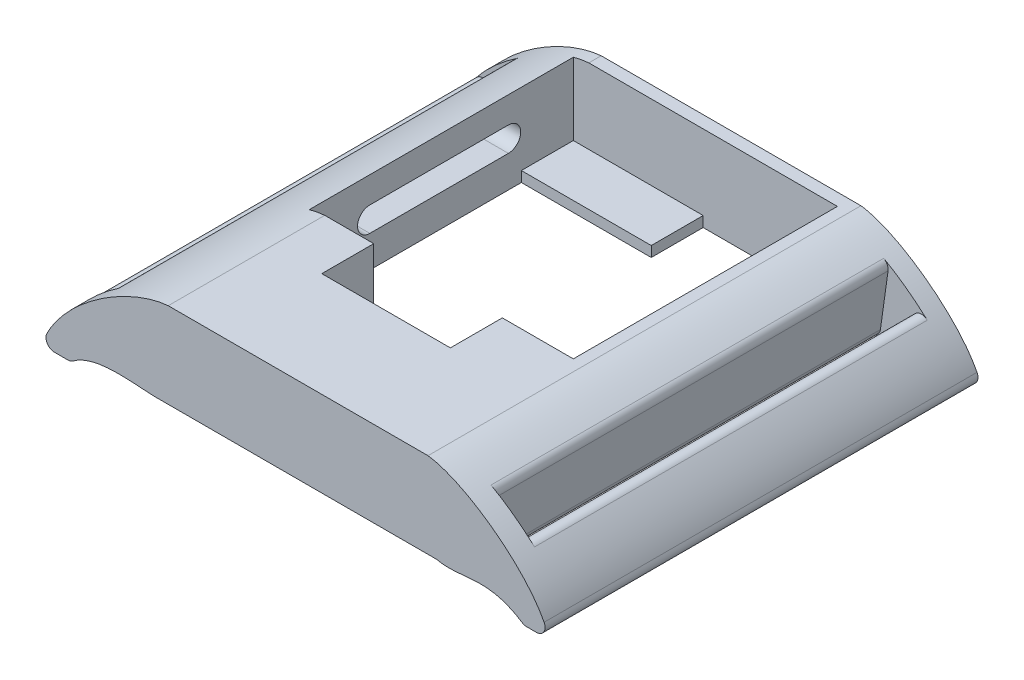
SolidWorks part; units mm, degrees
ref_plane "Front" through (0, 0, 0) normal (0, 0, 1) x (1, 0, 0)
ref_plane "Top" through (0, 0, 0) normal (0, 1, 0) x (1, 0, 0)
ref_plane "Right" through (0, 0, 0) normal (1, 0, 0) x (0, 0, -1)
sketch "Sketch1" plane through (0, 0, 0) normal (0, 0, 1) x (1, 0, 0)
  line L1 (-16, -5.0946) -> (16, -5.0946)
  line L3 (-15, 4.7762) -> (15, 4.7762)
  line L5 (-16, -5.0946) -> (15, 4.7762) construction
  line L6 (-15, 4.7762) -> (16, -5.0946) construction
  line L7 (-29.6051, -6.451) -> (-26.2487, -6.451)
  line L9 (26.1016, -6.6366) -> (28.994, -6.6366)
  spline S0 degree 3 poles (-15, 4.7762) (-19.8174, 4.3723) (-27.835, -0.8253) (-29.6051, -6.451) knots 0 0 0 0 1 1 1 1
  spline S1 degree 3 poles (-16, -5.0946) (-18.4717, -5.171) (-23.3925, -4.0435) (-26.2487, -6.451) knots 0 0 0 0 1 1 1 1
  spline S2 degree 3 poles (15, 4.7762) (19.5266, 4.2204) (27.6152, -1.736) (28.994, -6.6366) knots 0 0 0 0 1 1 1 1
  spline S3 degree 3 poles (16, -5.0946) (19.0102, -5.7784) (21.8339, -3.7083) (26.1016, -6.6366) knots 0 0 0 0 1 1 1 1
  point P0 (0, 0)
  point P10 (-31.6023, -5.5743)
  point P11 (-26.6956, -6.8299)
  point P12 (0, 0)
  point P13 (0, 0)
  point P14 (0, 0)
  point P15 (0, 0)
  point P16 (32.127, -12.9102)
  point P17 (0, 0)
  point P18 (0, 0)
  point P19 (28.994, -6.6366)
  point P20 (-29.6051, -6.451)
  point P21 (0, 0)
  point P22 (0, 4.7762)
  point P23 (0, -5.0946)
  dimension "D2" = 30
extrude "Boss-Extrude1" add sketch "Sketch1" along normal blind 50
fillet "Fillet1" radius 1 2 edges at (26.1016, -6.6366, 25) (-26.2487, -6.451, 25)
sketch "Sketch2" plane through (0, -5.0946, 0) normal (0, -1, 0) x (1, 0, 0)
  line L0 (-16.7915, 31.9252) -> (-9.3415, 31.9252)
  line L2 (13.7085, 31.9252) -> (13.7085, 1.4252)
  line L3 (13.7085, 1.4252) -> (-16.7915, 1.4252)
  line L4 (-16.7915, 31.9252) -> (-16.7915, 1.4252)
  line L5 (13.7085, 31.9252) -> (-16.7915, 1.4252) construction
  line L6 (13.7085, 1.4252) -> (-16.7915, 31.9252) construction
  line L8 (-9.3415, 31.9252) -> (-9.3415, 37.9252)
  line L9 (-9.3415, 37.9252) -> (5.5085, 37.9252)
  line L10 (5.5085, 31.9252) -> (5.5085, 37.9252)
  line L11 (5.5085, 31.9252) -> (13.7085, 31.9252)
  point P0 (-1.5415, 16.6752)
  dimension "D1" = 30.5
  dimension "D2" = 30.5
  dimension "D3" = 7.45
  dimension "D4" = 8.2
  dimension "D5" = 6
extrude "Cut-Extrude1" cut sketch "Sketch2" against normal blind 10 and the other way blind 0.1 contours L4 L3 L2 L11 L10 L9 L8 L0
ref_plane "Plane1" through (0.3705, -3.1974, 0) normal (0.1151, -0.9934, 0) x (-0.9934, -0.1151, 0)
ref_plane "Plane2" through (-0.392, -2.7998, 0) normal (-0.1386, -0.9903, 0) x (-0.9903, 0.1386, 0)
sketch "Sketch4" plane through (-0.392, -2.7998, 0) normal (-0.1386, -0.9903, 0) x (-0.9903, 0.1386, 0)
  line L1 (-19.8092, -47.4995) -> (-23.0955, -47.4995)
  line L2 (-19.8092, -47.4995) -> (-19.8092, -2.1451)
  line L3 (-19.8092, -2.1451) -> (-23.0955, -2.1451)
  line L4 (-23.0955, -47.4995) -> (-23.0955, -2.1451)
  point P4 (-20.8839, -47.3824)
  point P5 (-19.8092, -47.4995)
  dimension "D1" = 45.3545
extrude "Cut-Extrude3" cut sketch "Sketch4" against normal blind 59.6
fillet "Fillet2" radius 1 4 edges at (20.3715, 2.6365, 24.8223) (23.3944, 0.5266, 24.8223) (19.2855, -5.1211, 24.8223) (22.6011, -5.1404, 24.8223)
sketch "Sketch5" plane through (0.3705, -3.1974, 0) normal (0.1151, -0.9934, 0) x (-0.9934, -0.1151, 0)
  line L1 (25.997, -47.8859) -> (22.9745, -47.8859)
  line L2 (25.997, -47.8859) -> (25.997, -1.8859)
  line L3 (25.997, -1.8859) -> (22.9745, -1.8859)
  line L4 (22.9745, -47.8859) -> (22.9745, -1.8859)
  dimension "D1" = 46
extrude "Cut-Extrude4" cut sketch "Sketch5" against normal blind 59.6
fillet "Fillet3" radius 1 3 edges at (-23.2725, 1.245, 24.8859) (-22.5487, -5.0013, 24.8859) (-26.0465, -1.0743, 24.8859)
sketch "Sketch8" plane through (-16.7915, 0, 0) normal (1, 0, 0) x (0, 0, -1)
  line L0 (-24.9252, 0) -> (-8.9252, 0) construction
  line L1 (-24.9252, 1.42) -> (-8.9252, 1.42)
  line L2 (-24.9252, -1.42) -> (-8.9252, -1.42)
  line L3 (-31.9252, 4.4487) -> (-31.9252, -5.0869) construction
  arc A0 (-24.9252, 1.42) -> (-24.9252, -1.42) centre (-24.9252, 0) ccw
  arc A1 (-8.9252, -1.42) -> (-8.9252, 1.42) centre (-8.9252, 0) ccw
  point P3 (-16.9252, 0)
  dimension "D1" = 7
  dimension "D2" = 16
extrude "Cut-Extrude6" cut sketch "Sketch8" against normal blind 10
sketch "Sketch9" plane through (13.7085, 0, 0) normal (-1, 0, 0) x (0, 0, 1)
  line L1 (31.9252, -5.0946) -> (21.9252, -5.0946)
  line L2 (31.9252, -5.0946) -> (31.9252, -3.8946)
  line L3 (31.9252, -3.8946) -> (21.9252, -3.8946)
  line L4 (21.9252, -5.0946) -> (21.9252, -3.8946)
  dimension "D1" = 1.2
  dimension "D2" = 10
extrude "Boss-Extrude3" add sketch "Sketch9" along normal blind 8
fillet "Fillet4" radius 1 2 edges at (28.994, -6.6366, 25) (-29.6051, -6.451, 25)
sketch "Sketch12" plane through (-16.7915, 0, 0) normal (1, 0, 0) x (0, 0, -1)
  line L1 (-1.4252, -5.0869) -> (-7.4252, -5.0869)
  line L2 (-1.4252, -5.0869) -> (-1.4252, -3.8869)
  line L3 (-1.4252, -3.8869) -> (-7.4252, -3.8869)
  line L4 (-7.4252, -5.0869) -> (-7.4252, -3.8869)
  point P5 (0, 0)
extrude "Boss-Extrude5" add sketch "Sketch12" along normal blind 15
